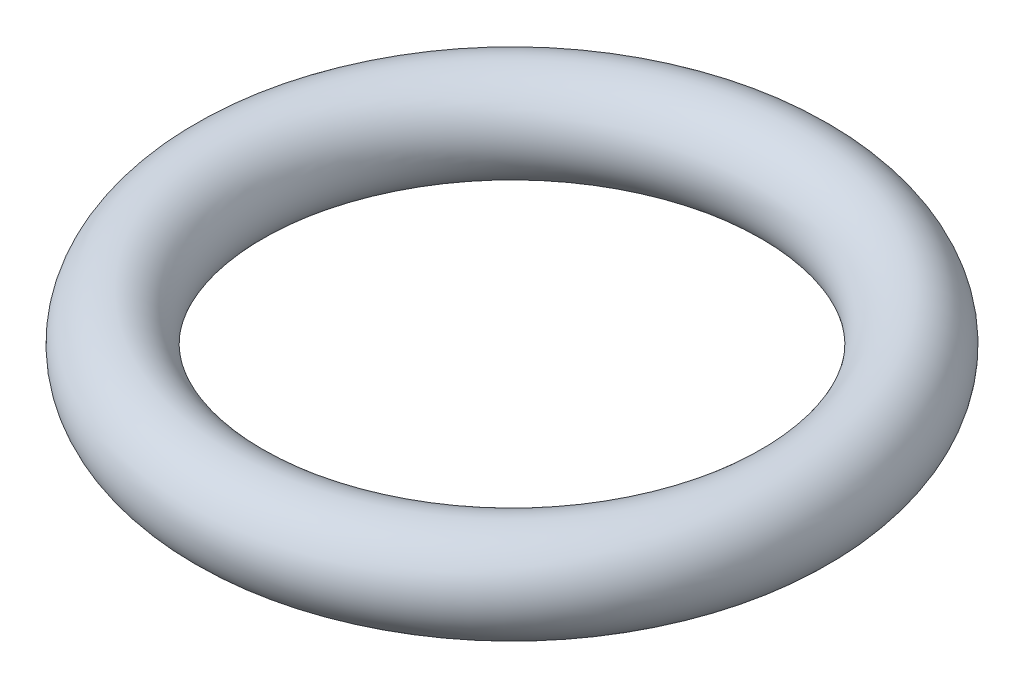
SolidWorks part; units mm, degrees
ref_plane "Front Plane" through (0, 0, 0) normal (0, 0, 1) x (1, 0, 0)
ref_plane "Top Plane" through (0, 0, 0) normal (0, 1, 0) x (1, 0, 0)
ref_plane "Right Plane" through (0, 0, 0) normal (1, 0, 0) x (0, 0, -1)
sketch "Sketch2" plane through (0, 0, 0) normal (0, 0, 1) x (1, 0, 0)
  line L0 (0, 0) -> (0, 56.2644)
  line L1 (0, -55) -> (0, 55) construction
  line L2 (55, 0) -> (-55, 0) construction
  circle A0 centre (-152.4, 0) radius 25.4
  dimension "D2" = 50.8
  dimension "D1" = 56.2644
  dimension "D3" = 152.4
revolve "Revolve1" add sketch "Sketch2" angle 360 about L0
